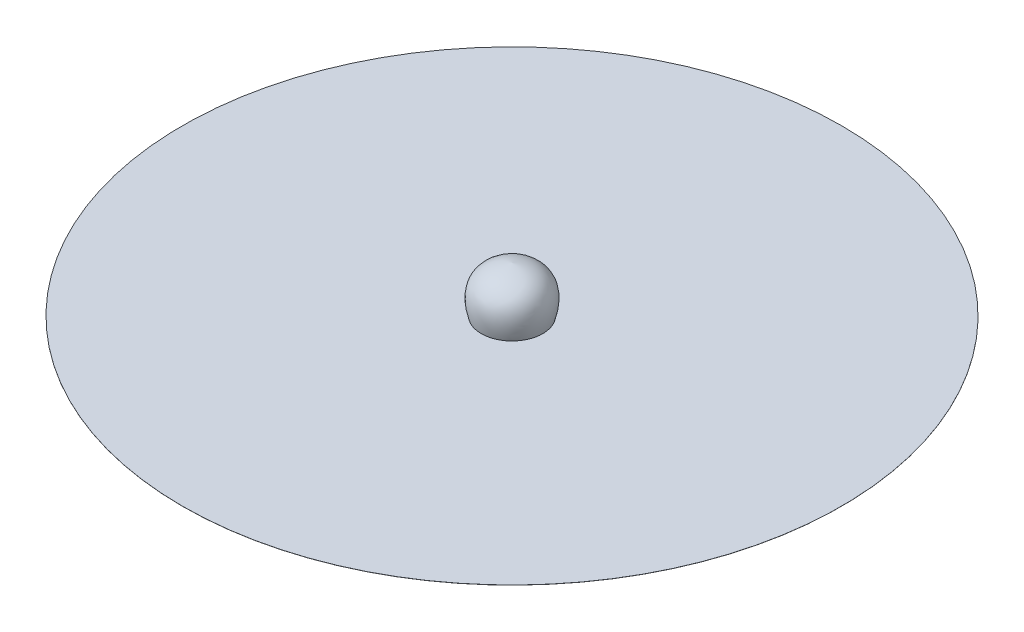
SolidWorks part; units mm, degrees
ref_plane "Front Plane" through (0, 0, 0) normal (0, 0, 1) x (1, 0, 0)
ref_plane "Top Plane" through (0, 0, 0) normal (0, 1, 0) x (1, 0, 0)
ref_plane "Right Plane" through (0, 0, 0) normal (1, 0, 0) x (0, 0, -1)
sketch "Sketch1" plane through (0, 0, 0) normal (0, 1, 0) x (1, 0, 0)
  circle A0 centre (0, 0) radius 27500
  dimension "D1" = 55000
extrude "Boss-Extrude1" add sketch "Sketch1" along normal mid plane 10
sketch "Sketch3" plane through (0, 0, 0) normal (0, 0, 1) x (1, 0, 0)
  line L0 (27500, 5) -> (-27500, 5) construction
  line L1 (0, 0) -> (0, 8536.61) construction
  spline S0 degree 2 poles (-2567.169, 5) (-3536.2303, 3379.5982) (0, 3835.2886) knots 0 0 0 1 1 1
surface "Surface-Revolve1" sketch "Sketch3" parameters "D1"=360
